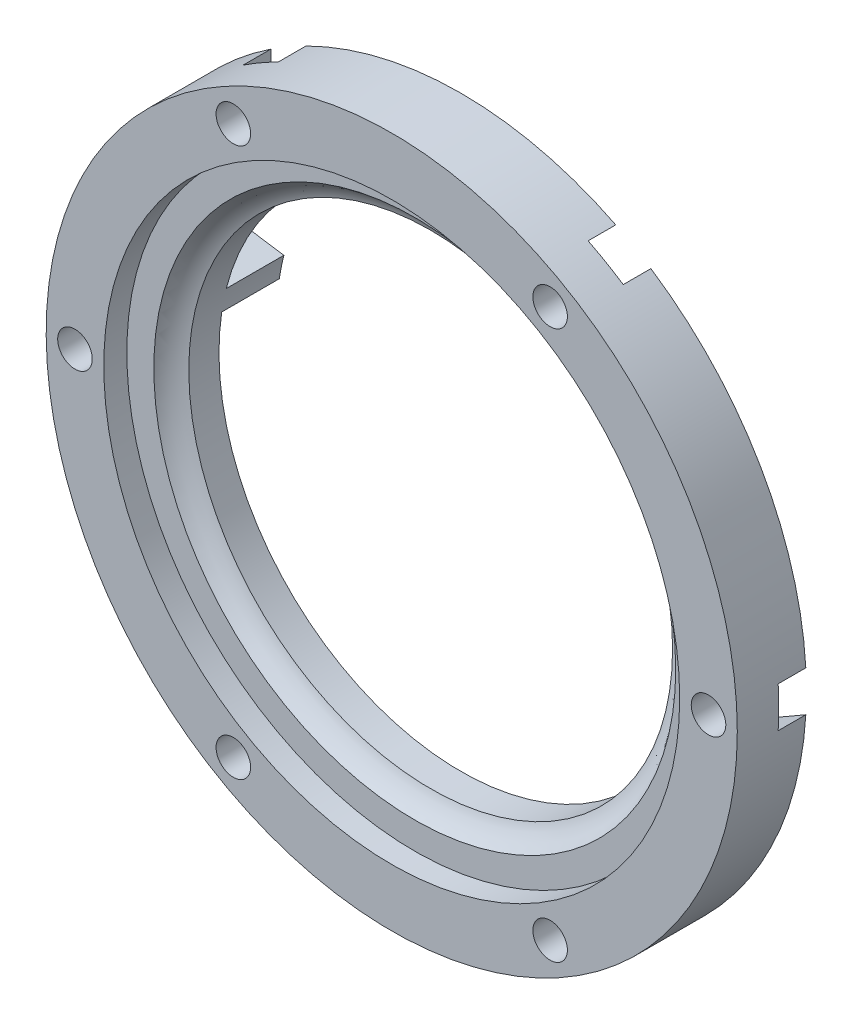
SolidWorks part; units mm, degrees
ref_plane "Piano frontale" through (0, 0, 0) normal (0, 0, 1) x (1, 0, 0)
ref_plane "Piano superiore" through (0, 0, 0) normal (0, 1, 0) x (1, 0, 0)
ref_plane "Piano destro" through (0, 0, 0) normal (1, 0, 0) x (0, 0, -1)
sketch "Schizzo1" plane through (0, 0, 0) normal (0, 0, 1) x (1, 0, 0)
  circle A0 centre (0, 0) radius 21
  circle A1 centre (0, 0) radius 30
  dimension "D1" = 42
  dimension "D2" = 60
extrude "Estrusione-Estrusione1" add sketch "Schizzo1" along normal blind 4
ref_axis "Assi1" through (0, 0, 4) along (0, 0, -1)
sketch "Schizzo2" plane through (0, 0, 0) normal (1, 0, 0) x (0, 0, -1)
  line L0 (-4, 30) -> (-4, -30) construction
  circle A0 centre (-5.5, 20) radius 3.05
  dimension "D1" = 6.1
  dimension "D2" = 20
  dimension "D3" = 1.5
revolve "Taglia-Rivoluzione1" cut sketch "Schizzo2" angle 360 about axis through (0, 0, 4) along (0, 0, -1)
sketch "Schizzo3" plane through (0, 0, 4) normal (0, 0, 1) x (1, 0, 0)
  circle A0 centre (0, 0) radius 25
  circle A1 centre (0, 0) radius 30
  dimension "D1" = 50
extrude "Estrusione-Estrusione2" add sketch "Schizzo3" along normal blind 2
sketch "Schizzo4" plane through (0, 0, 0) normal (0, 0, 1) x (1, 0, 0)
  circle A0 centre (0, 0) radius 27.5 construction
  circle A2 centre (-27.5, 0) radius 1.5
  dimension "D1" = 55
  dimension "D2" = 3
extrude "Taglio-Estrusione1" cut sketch "Schizzo4" against normal through all and the other way through all contours A2
sketch "Schizzo5" plane through (0, 0, 0) normal (0, 0, -1) x (-1, 0, 0)
  line L1 (30.25, 1.5877) -> (27.5, 3.1754)
  line L2 (27.5, 3.1754) -> (24.75, 1.5877)
  line L3 (24.75, 1.5877) -> (24.75, -1.5877)
  line L4 (24.75, -1.5877) -> (27.5, -3.1754)
  line L5 (27.5, -3.1754) -> (30.25, -1.5877)
  line L6 (30.25, -1.5877) -> (30.25, 1.5877)
  circle A0 centre (27.5, 0) radius 2.75 construction
  dimension "D1" = 5.5
extrude "Taglio-Estrusione2" cut sketch "Schizzo5" against normal blind 2.4
pattern_circular "RipetizioneCircolare1" count 6 over 360 about axis through (0, 0, 0) along (0, 0, 1) of "Taglio-Estrusione1", "Taglio-Estrusione2"
sketch "Schizzo6" plane through (0, 0, 0) normal (0, 0, -1) x (-1, 0, 0)
  line L0 (20.7608, 3.1609) -> (29.6582, 4.5155)
  line L1 (0, 0) -> (29.6582, 4.5155) construction
  line L2 (20.3653, 5.1237) -> (29.2912, 6.4827)
  arc A0 (29.2912, 6.4827) -> (29.6582, 4.5155) centre (0, 0) cw
  arc A1 (20.3653, 5.1237) -> (20.7608, 3.1609) centre (0, 0) cw
  arc A2 (29.9482, 1.7619) -> (16.5, 25.0549) centre (0, 0) ccw construction
  arc A3 (-16.5, 25.0549) -> (-29.9482, 1.7619) centre (0, 0) ccw construction
  circle A4 centre (0, 0) radius 21 construction
  dimension "D1" = 1
  dimension "D2" = 2
extrude "Estrusione-Estrusione3" add sketch "Schizzo6" along normal blind 5
